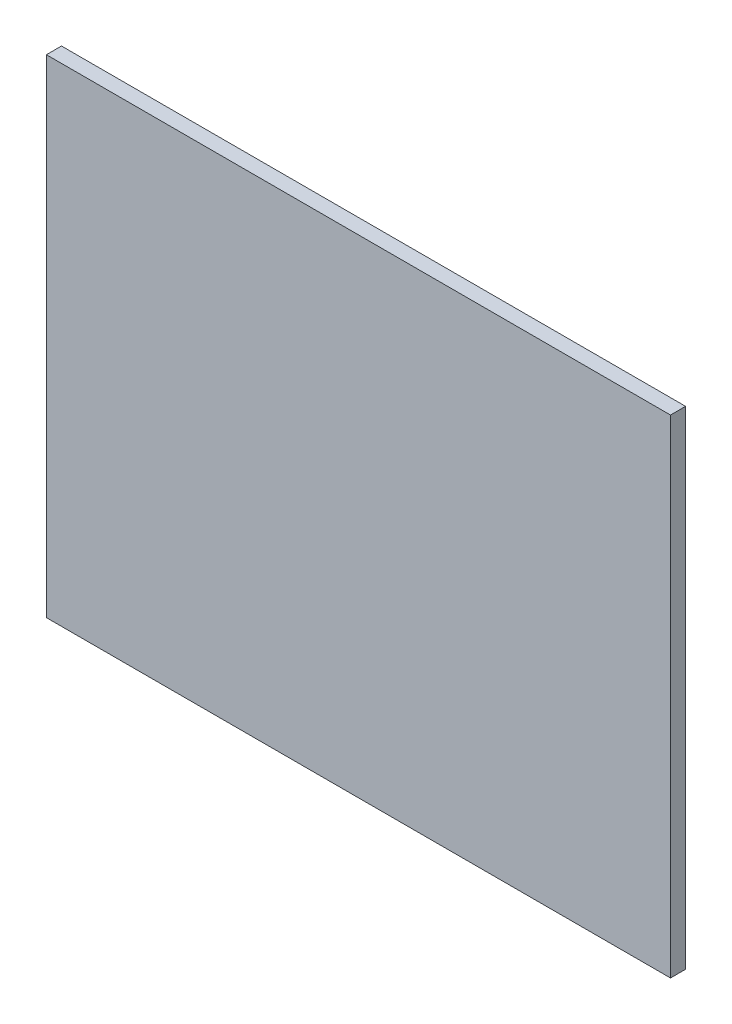
SolidWorks part; units mm, degrees
ref_plane "Front Plane" through (0, 0, 0) normal (0, 0, 1) x (1, 0, 0)
ref_plane "Top Plane" through (0, 0, 0) normal (0, 1, 0) x (1, 0, 0)
ref_plane "Right Plane" through (0, 0, 0) normal (1, 0, 0) x (0, 0, -1)
sketch "Sketch1" plane through (0, 0, 0) normal (0, 0, 1) x (1, 0, 0)
  line L1 (372.5, -291) -> (-372.5, -291)
  line L2 (372.5, -291) -> (372.5, 291)
  line L3 (372.5, 291) -> (-372.5, 291)
  line L4 (-372.5, -291) -> (-372.5, 291)
  line L5 (372.5, -291) -> (-372.5, 291) construction
  line L6 (372.5, 291) -> (-372.5, -291) construction
  point P0 (0, 0)
  dimension "D1" = 582
  dimension "D2" = 745
extrude "Boss-Extrude1" add sketch "Sketch1" along normal blind 18
equation "\"H_DSP\"=18"
equation "\"D1@Boss-Extrude1\"=\"H_DSP\""
